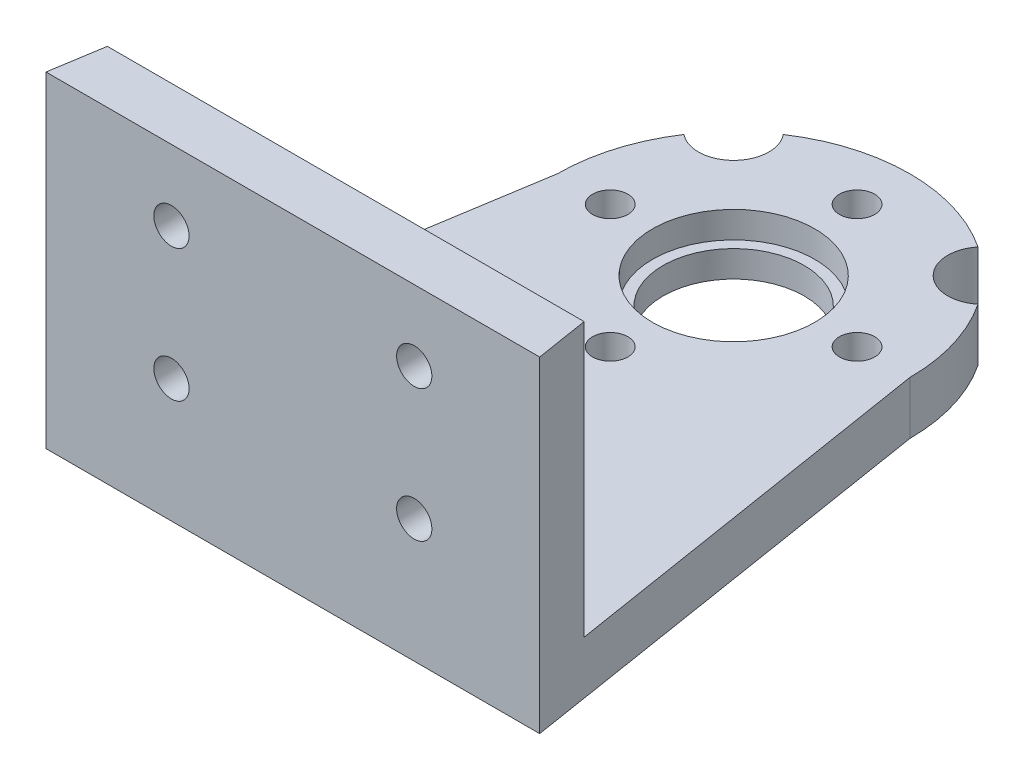
SolidWorks part; units mm, degrees
material "Custom Plastic"
ref_plane "Front Plane" through (0, 0, 0) normal (0, 0, 1) x (1, 0, 0)
ref_plane "Top Plane" through (0, 0, 0) normal (0, 1, 0) x (1, 0, 0)
ref_plane "Right Plane" through (0, 0, 0) normal (1, 0, 0) x (0, 0, -1)
sketch "Sketch1" plane through (0, 0, 0) normal (0, 1, 0) x (1, 0, 0)
  line L0 (-10, 0) -> (-14, -25)
  line L1 (10, 0) -> (14, -25)
  line L2 (0, 17.2103) -> (0, -39.4896) construction
  line L3 (-14, -25) -> (14, -25)
  arc A0 (-10, 0) -> (10, 0) centre (0, 0) cw
  dimension "D1" = 10
  dimension "D2" = 25
  dimension "D3" = 14
extrude "Boss-Extrude1" add sketch "Sketch1" along normal blind 3
sketch "Sketch2" plane through (0, 3, 0) normal (0, 1, 0) x (1, 0, 0)
  line L0 (-21.4034, 0) -> (30.5216, 0) construction
  circle A0 centre (0, 0) radius 4
  dimension "D1" = 8
extrude "Cut-Extrude1" cut sketch "Sketch2" against normal blind 13
sketch "Sketch3" plane through (0, 3, 0) normal (0, 1, 0) x (1, 0, 0)
  line L0 (0, 14.8087) -> (0, -39.0944) construction
  line L1 (-14, -25) -> (14, -25) construction
  line L2 (-10, 0) -> (0, 0) construction
  line L3 (-13.04, -19) -> (0, -19) construction
  line L4 (-10, 0) -> (-14, -25) construction
  line L5 (14, -25) -> (10, 0) construction
  circle A0 centre (-6.52, -19) radius 1
  circle A1 centre (6.52, -19) radius 1
  circle A2 centre (0, -19) radius 1
  point P3 (-6.52, -19)
  point P11 (-13.04, -19)
  point P12 (13.0353, -18.9708)
  point P18 (0, -19)
  dimension "D3" = 2
  dimension "D2" = 2
  dimension "D1" = 6
extrude "Cut-Extrude2" cut sketch "Sketch3" against normal blind 13
sketch "Sketch4" plane through (0, 3, 0) normal (0, 1, 0) x (1, 0, 0)
  line L0 (0, 11.5358) -> (0, -14.2328) construction
  circle A0 centre (0, -7) radius 1
  circle A1 centre (-7, 0) radius 1
  circle A2 centre (0, 7) radius 1
  circle A3 centre (7, 0) radius 1
  point P0 (0, -7)
  point P15 (0, 0)
  dimension "D2" = 2
  dimension "D1" = 7
  dimension "D3" = 4
extrude "Cut-Extrude3" cut sketch "Sketch4" against normal up to vertex (3 mm away) up to point (0, 0, 0)
sketch "Sketch5" plane through (0, 3, 0) normal (0, 1, 0) x (1, 0, 0)
  line L0 (-13.52, -22) -> (13.52, -22)
  line L1 (-10, 0) -> (-14, -25) construction
  line L2 (14, -25) -> (10, 0) construction
  line L3 (-13.52, -22) -> (-14, -25)
  line L4 (-14, -25) -> (14, -25)
  line L5 (14, -25) -> (13.52, -22)
  dimension "D1" = 3
extrude "Boss-Extrude2" add sketch "Sketch5" along normal blind 15.5
sketch "Sketch6" plane through (0, 3, 0) normal (0, 1, 0) x (1, 0, 0)
  circle A0 centre (0, 0) radius 4.6
  dimension "D1" = 9.2
extrude "Cut-Extrude4" cut sketch "Sketch6" against normal blind 1.5
sketch "Sketch7" plane through (0, 3, 0) normal (0, 1, 0) x (1, 0, 0)
  line L0 (0, 12.0905) -> (0, -12.7025) construction
  line L1 (-13.0501, 13.0501) -> (0, 0) construction
  circle A0 centre (-7.0711, 7.0711) radius 2
  arc A1 (10, 0) -> (-10, 0) centre (0, 0) ccw construction
  circle A2 centre (7.0711, 7.0711) radius 2
  dimension "D1" = 4
extrude "Cut-Extrude5" cut sketch "Sketch7" against normal blind 10
sketch "Sketch8" plane through (0, 0, 22) normal (0, 0, -1) x (-1, 0, 0)
  line L0 (-13.52, 3) -> (13.52, 3) construction
  line L1 (-13.52, 18.5) -> (-13.52, 3) construction
  circle A0 centre (6.885, 7) radius 1
  circle A1 centre (-6.885, 7) radius 1
  circle A2 centre (6.885, 14.5) radius 1
  circle A3 centre (-6.885, 14.5) radius 1
  dimension "D1" = 2
  dimension "D2" = 2
  dimension "D3" = 13.77
  dimension "D4" = 4
  dimension "D6" = 6.635
  dimension "D5" = 2
extrude "Cut-Extrude6" cut sketch "Sketch8" against normal blind 10
